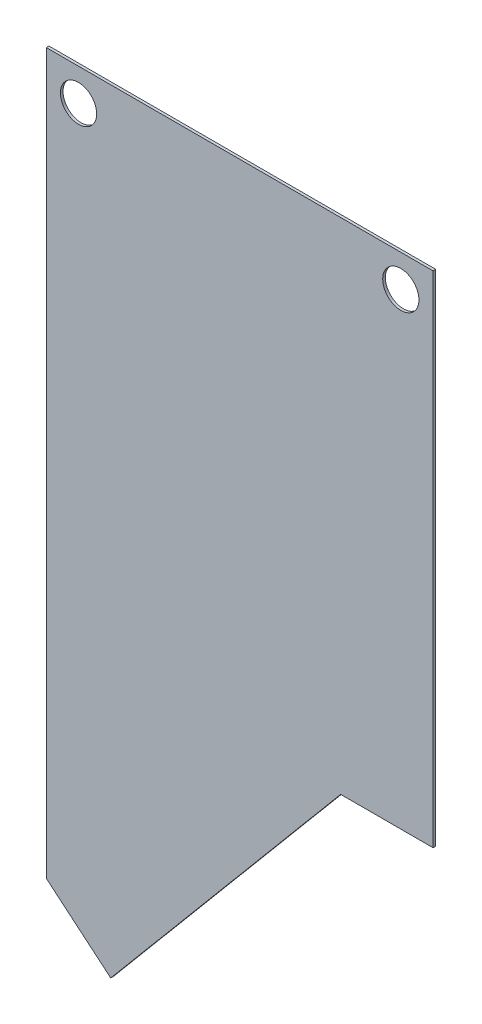
SolidWorks part; units mm, degrees
material "Acrylic (Medium-high impact)"
ref_plane "Front Plane" through (0, 0, 0) normal (0, 0, 1) x (1, 0, 0)
ref_plane "Top Plane" through (0, 0, 0) normal (0, 1, 0) x (1, 0, 0)
ref_plane "Right Plane" through (0, 0, 0) normal (1, 0, 0) x (0, 0, -1)
sketch "Sketch1" plane through (0, 0, 0) normal (0, 0, 1) x (1, 0, 0)
  line L1 (-50.8, 0) -> (254, 0)
  line L2 (-50.8, 0) -> (-50.8, -635)
  line L3 (-50.8, -635) -> (254, -635)
  line L4 (254, 0) -> (254, -635)
  dimension "D1" = 635
extrude "Boss-Extrude1" add sketch "Sketch1" along normal blind 2.1082
sketch "Sketch3" plane through (0, 0, 0) normal (0, 0, -1) x (-1, 0, 0)
  circle A1 centre (25.4, -25.4) radius 14.2875
extrude "Cut-Extrude2" cut sketch "Sketch3" against normal blind 2.1082
sketch "Sketch4" plane through (0, 0, 0) normal (0, 0, -1) x (-1, 0, 0)
  circle A0 centre (-228.6, -25.4) radius 14.2875
extrude "Cut-Extrude3" cut sketch "Sketch4" against normal blind 2.1082
sketch "Sketch5" plane through (0, 0, 0) normal (0, 0, -1) x (-1, 0, 0)
  line L1 (50.8, -635) -> (-254, -635) construction
  line L2 (-254, -635) -> (-254, -393.7)
  line L4 (50.8, -635) -> (50.8, -566.9737)
  line L11 (50.8, -566.9737) -> (0, -609.6)
  line L12 (50.8, -635) -> (-254, -635)
  line L13 (0, -609.6) -> (-181.1702, -393.7)
  line L14 (50.8, -393.7) -> (-254, -393.7) construction
  line L15 (-181.1702, -393.7) -> (0, -609.305) construction
  line L16 (-181.1702, -393.7) -> (-254, -393.7)
extrude "Cut-Extrude4" cut sketch "Sketch5" against normal through all
